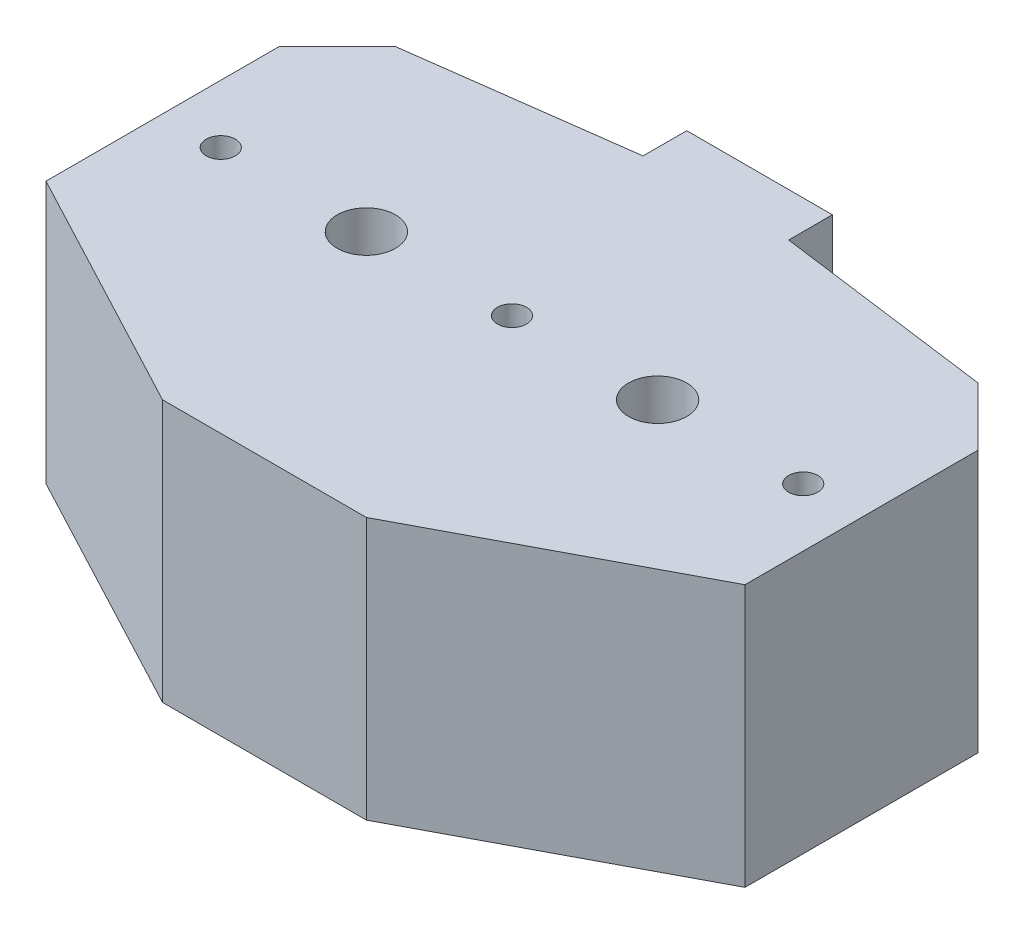
SolidWorks part; units mm, degrees
ref_plane "Спереди" through (0, 0, 0) normal (0, 0, 1) x (1, 0, 0)
ref_plane "Сверху" through (0, 0, 0) normal (0, 1, 0) x (1, 0, 0)
ref_plane "Справа" through (0, 0, 0) normal (1, 0, 0) x (0, 0, -1)
sketch "Эскиз1" plane through (0, 0, 0) normal (0, 1, 0) x (1, 0, 0)
  line L3 (24, 8) -> (24, -8)
  line L4 (24, -8) -> (7, -17)
  line L5 (7, -17) -> (-7, -17)
  line L6 (-7, -17) -> (-24, -8)
  line L7 (-24, -8) -> (-24, 8)
  line L10 (20, 12) -> (24, 8)
  line L11 (-24, 8) -> (-20, 12)
  line L12 (-5, 17) -> (5, 17)
  line L13 (-5, 17) -> (-5, 14)
  line L14 (5, 17) -> (5, 14)
  line L15 (-20, 12) -> (-5, 14)
  line L16 (5, 14) -> (20, 12)
  circle A0 centre (0, 0) radius 1
  circle A1 centre (20, 0) radius 1
  circle A2 centre (-20, 0) radius 1
  circle A3 centre (-10, 0) radius 2
  circle A4 centre (10, 0) radius 2
  dimension "D1" = 2
  dimension "D3" = 2
  dimension "D2" = 2
extrude "Бобышка-Вытянуть1" add sketch "Эскиз1" along normal blind 18
